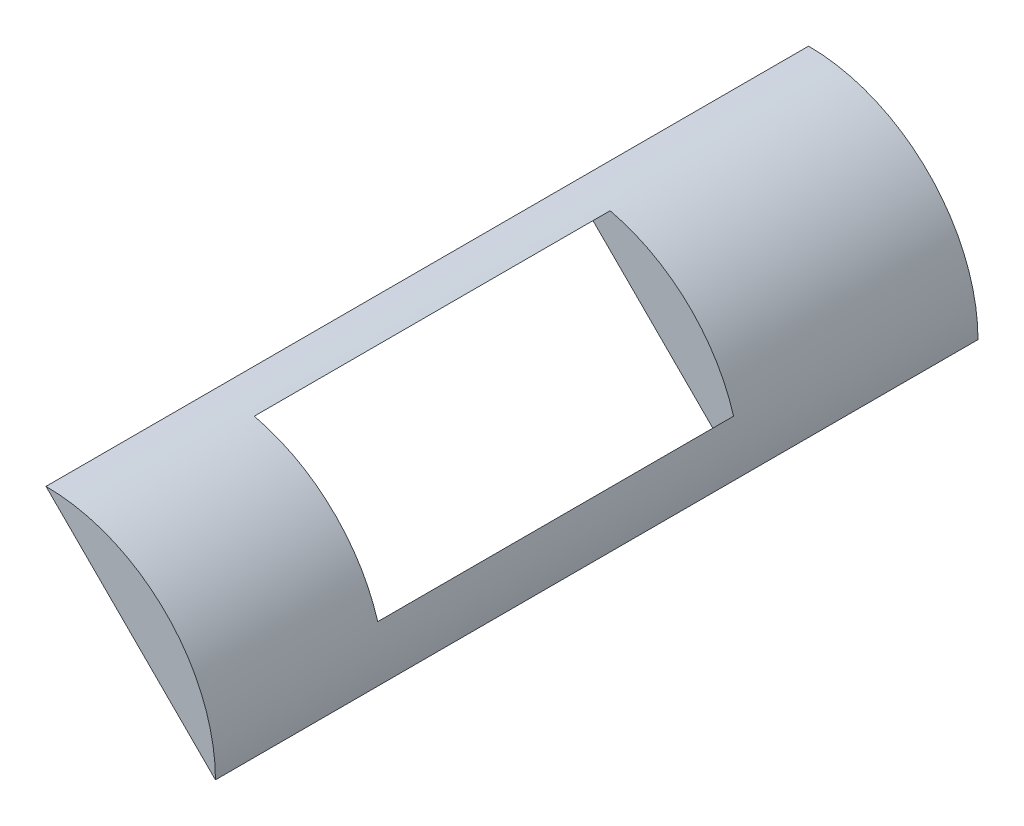
SolidWorks part; units mm, degrees
ref_plane "Płaszczyzna przednia" through (0, 0, 0) normal (0, 0, 1) x (1, 0, 0)
ref_plane "Płaszczyzna górna" through (0, 0, 0) normal (0, 1, 0) x (1, 0, 0)
ref_plane "Płaszczyzna prawa" through (0, 0, 0) normal (1, 0, 0) x (0, 0, -1)
sketch "Szkic1" plane through (0, 0, 0) normal (0, 0, 1) x (1, 0, 0)
  line L0 (0, 0) -> (0, 10)
  line L1 (0, 0) -> (10, 0)
  arc A0 (10, 0) -> (0, 10) centre (0, 0) ccw
  dimension "D1" = 20
extrude "Dodanie-wyciągnięcie1" add sketch "Szkic1" along normal blind 45
sketch "Szkic2" plane through (0, 0, 45) normal (0, 0, 1) x (1, 0, 0)
  line L0 (0, 10) -> (10, 0)
  line L1 (10, 0) -> (0, 0)
  line L2 (0, 0) -> (0, 10)
extrude "Wytnij-wyciągnięcie1" cut sketch "Szkic2" against normal blind 60
sketch "Szkic4" plane through (5, 5, 0) normal (-0.7071, -0.7071, 0) x (0, 0, 1)
  line L0 (45, -7.0711) -> (45, 7.0711) construction
  line L1 (14, 5.2622) -> (35, 5.2622)
  line L2 (14, 5.2622) -> (14, -4.7378)
  line L3 (14, -4.7378) -> (35, -4.7378)
  line L4 (35, 5.2622) -> (35, -4.7378)
  dimension "D1" = 21
  dimension "D2" = 10
  dimension "D3" = 10
extrude "Wytnij-wyciągnięcie2" cut sketch "Szkic4" against normal blind 60
